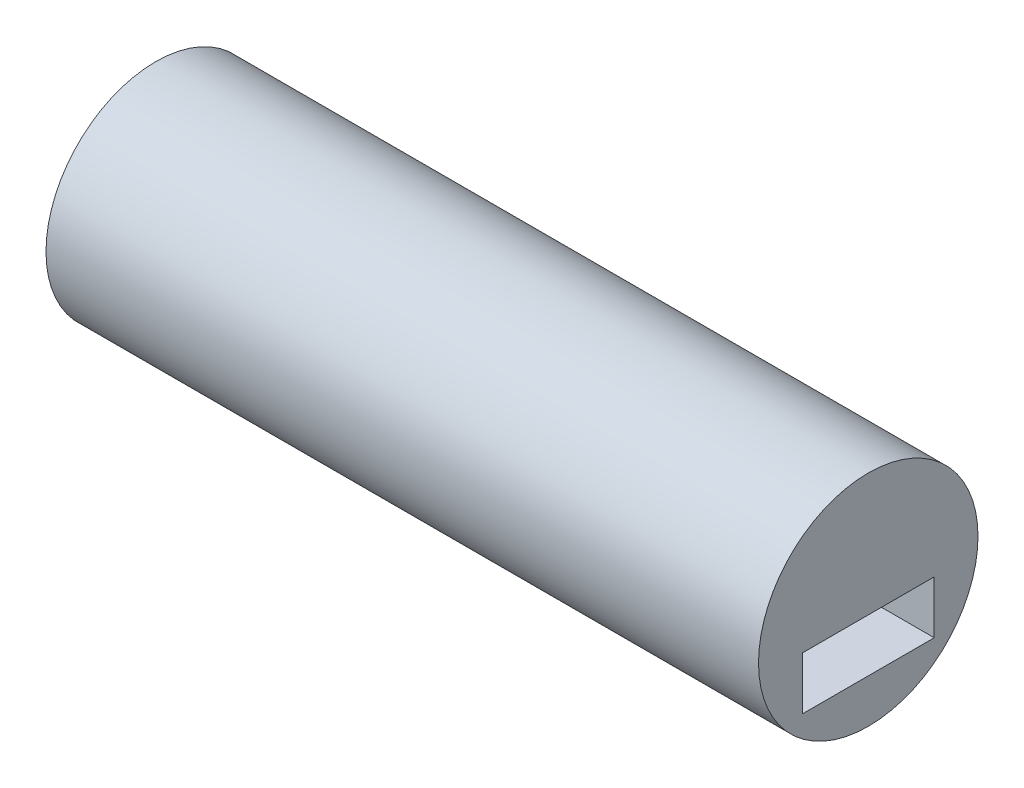
SolidWorks part; units mm, degrees
ref_plane "Front Plane" through (0, 0, 0) normal (0, 0, 1) x (1, 0, 0)
ref_plane "Top Plane" through (0, 0, 0) normal (0, 1, 0) x (1, 0, 0)
ref_plane "Right Plane" through (0, 0, 0) normal (1, 0, 0) x (0, 0, -1)
sketch "Sketch1" plane through (0, 0, 0) normal (1, 0, 0) x (0, 0, -1)
  line L1 (-50, -50) -> (50, -50)
  line L2 (-50, -50) -> (-50, -10)
  line L3 (-50, -10) -> (50, -10)
  line L4 (50, -50) -> (50, -10)
  circle A0 centre (0, 0) radius 93.1728
  dimension "D1" = 186.3457
  dimension "D2" = 100
  dimension "D3" = 40
  dimension "D6" = 50
  dimension "D7" = 10
extrude "Boss-Extrude1" add sketch "Sketch1" along normal blind 540
sketch "Sketch2" plane through (540, 0, 0) normal (1, 0, 0) x (0, 0, -1)
  circle A0 centre (0, 0) radius 83.1728
  circle A1 centre (0, 0) radius 93.1728 construction
  dimension "D1" = 10
extrude "Cut-Extrude2" cut sketch "Sketch2" against normal through all flip side to cut
